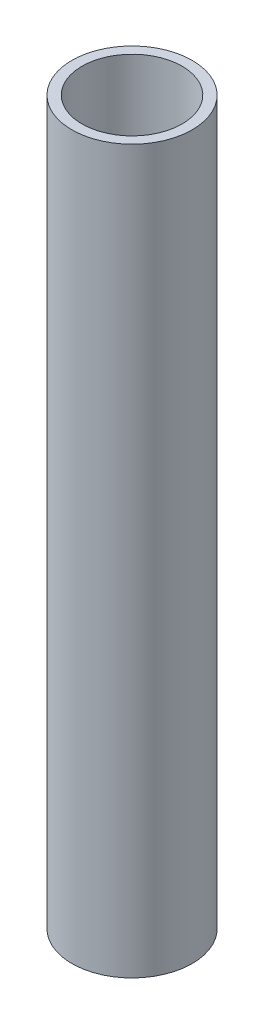
SolidWorks part; units mm, degrees
ref_plane "Front Plane" through (0, 0, 0) normal (0, 0, 1) x (1, 0, 0)
ref_plane "Top Plane" through (0, 0, 0) normal (0, 1, 0) x (1, 0, 0)
ref_plane "Right Plane" through (0, 0, 0) normal (1, 0, 0) x (0, 0, -1)
sketch "Sketch3" plane through (0, 0, 0) normal (0, 0, 1) x (1, 0, 0)
  line L0 (-669.0269, -748.7421) -> (-669.0269, -824.9421)
other "Pipe 0.5 SCH 40(5)"
ref_plane "Plane1" through (-669.0269, -748.7421, 0) normal (0, -1, 0) x (1, 0, 0)
sketch "Sketch1" plane through (-669.0269, -748.7421, 0) normal (0, -1, 0) x (1, 0, 0)
  circle A0 centre (0, 0) radius 5.2832
  circle A1 centre (0, 0) radius 6.35
  point P5 (0, 0)
  dimension "In_dia" = 10.5664
  dimension "Out_dia" = 12.7
